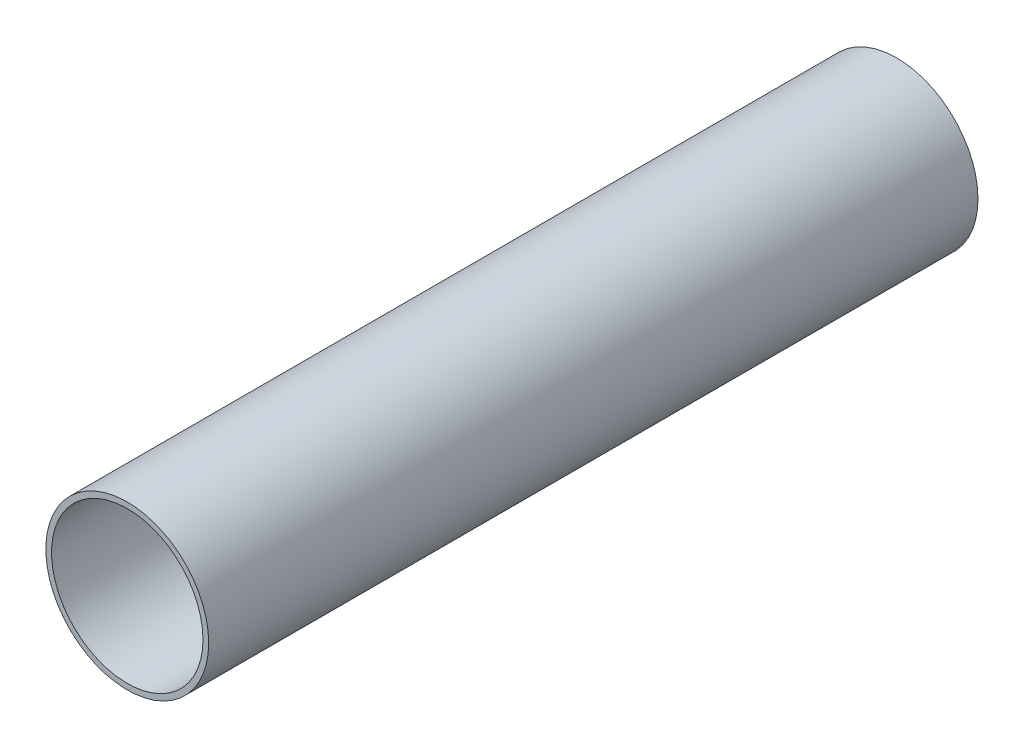
SolidWorks part; units mm, degrees
material "Papel"
ref_plane "Plano frontal" through (0, 0, 0) normal (0, 0, 1) x (1, 0, 0)
ref_plane "Plano superior" through (0, 0, 0) normal (0, 1, 0) x (1, 0, 0)
ref_plane "Plano direito" through (0, 0, 0) normal (1, 0, 0) x (0, 0, -1)
sketch "Esboço1" plane through (0, 0, 0) normal (0, 0, 1) x (1, 0, 0)
  line L0 (0, 0) -> (-8773.2291, 0) construction
  line L1 (0, -175.4646) -> (0, 8597.7645) construction
  circle A0 centre (0, 0) radius 26.575
  circle A1 centre (0, 0) radius 28.575
  dimension "D2" = 57.15
  dimension "D1" = 2
extrude "Ressalto-extrusão1" add sketch "Esboço1" along normal blind 270
equation "\"D2@Esboço1\"=25.4*(2.5-2*(1/8))"
